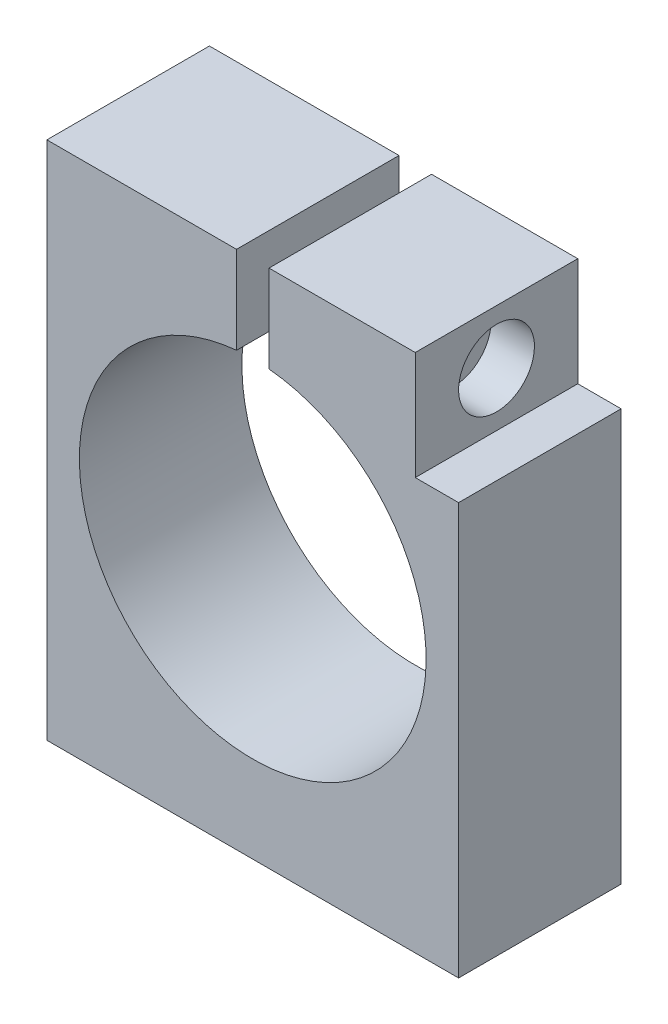
SolidWorks part; units mm, degrees
ref_plane "Plan de face" through (0, 0, 0) normal (0, 0, 1) x (1, 0, 0)
ref_plane "Plan de dessus" through (0, 0, 0) normal (0, 1, 0) x (1, 0, 0)
ref_plane "Plan de droite" through (0, 0, 0) normal (1, 0, 0) x (0, 0, -1)
sketch "Esquisse1" plane through (0, 0, 0) normal (0, 0, 1) x (1, 0, 0)
  line L0 (8.1425, 19) -> (8.1425, 9)
  line L1 (-25.8575, 19) -> (8.1425, 19)
  line L2 (-25.8575, 19) -> (-25.8575, -29)
  line L3 (-25.8575, -29) -> (12.1425, -29)
  line L4 (12.1425, 9) -> (12.1425, -29)
  line L5 (8.1425, 9) -> (12.1425, 9)
  line L6 (-5.3543, 19) -> (-5.3543, 10.9292)
  line L7 (-8.3543, 19) -> (-8.3543, 10.9298)
  circle A0 centre (-6.8575, -5) radius 16
  point P8 (-6.8543, 19)
  point P9 (-40.448, 35.1108)
  dimension "D3" = 19
  dimension "D7" = 32
  dimension "D1" = 10
  dimension "D2" = 4
  dimension "D4" = 19
  dimension "D5" = 24
  dimension "D6" = 48
  dimension "D8" = 1.5
  dimension "D9" = 1.5
extrude "Boss.-Extru.1" add sketch "Esquisse1" along normal blind 15 contours A0 L7 L1 L2 L3 L4 L5 L0 L6
sketch "Esquisse2" plane through (8.1425, 0, 0) normal (1, 0, 0) x (0, 0, -1)
  line L0 (-15, 19) -> (0, 19) construction
  line L2 (-15, 19) -> (-15, 9) construction
  circle A0 centre (-7.5, 14) radius 3.5
  dimension "D1" = 7
  dimension "D3" = 7.5
  dimension "D2" = 5
extrude "Enlèv. mat.-Extru.1" cut sketch "Esquisse2" against normal blind 4
sketch "Esquisse5" plane through (4.1425, 0, 0) normal (1, 0, 0) x (0, 0, -1)
  circle A0 centre (-7.5, 14) radius 1.75
  circle A3 centre (-7.5, 14) radius 3.5 construction
  dimension "D1" = 3.5
  dimension "D3" = 0
extrude "Enlèv. mat.-Extru.2" cut sketch "Esquisse5" against normal blind 20
